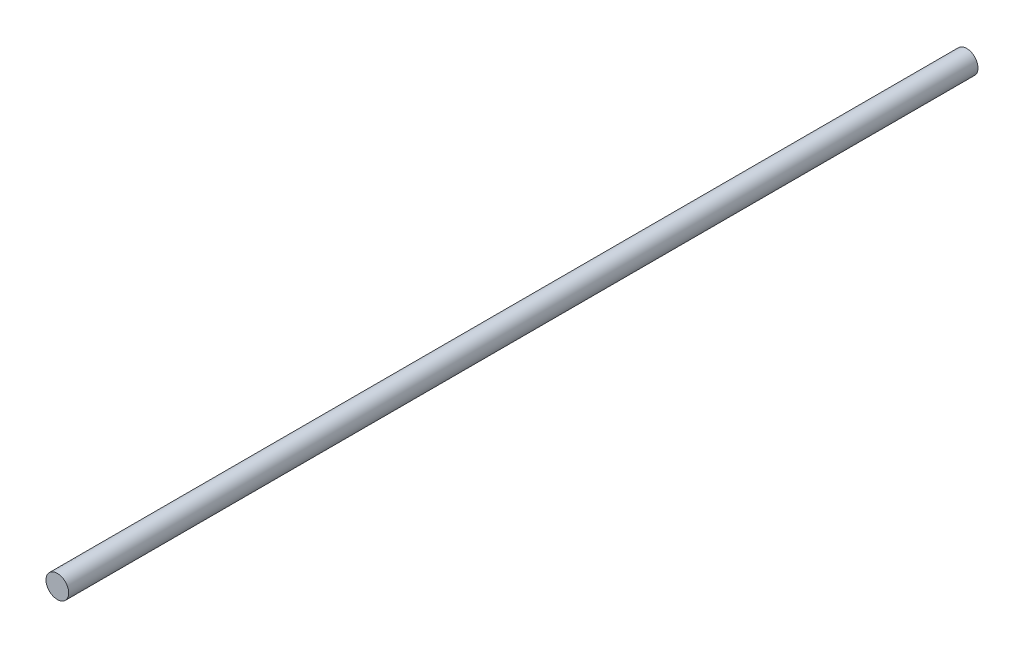
SolidWorks part; units mm, degrees
ref_plane "Front Plane" through (0, 0, 0) normal (0, 0, 1) x (1, 0, 0)
ref_plane "Top Plane" through (0, 0, 0) normal (0, 1, 0) x (1, 0, 0)
ref_plane "Right Plane" through (0, 0, 0) normal (1, 0, 0) x (0, 0, -1)
sketch "Sketch1" plane through (0, 0, 0) normal (0, 0, 1) x (1, 0, 0)
  circle A0 centre (0, 0) radius 6.35
  dimension "D1" = 12.7
extrude "Boss-Extrude1" add sketch "Sketch1" along normal blind 508
